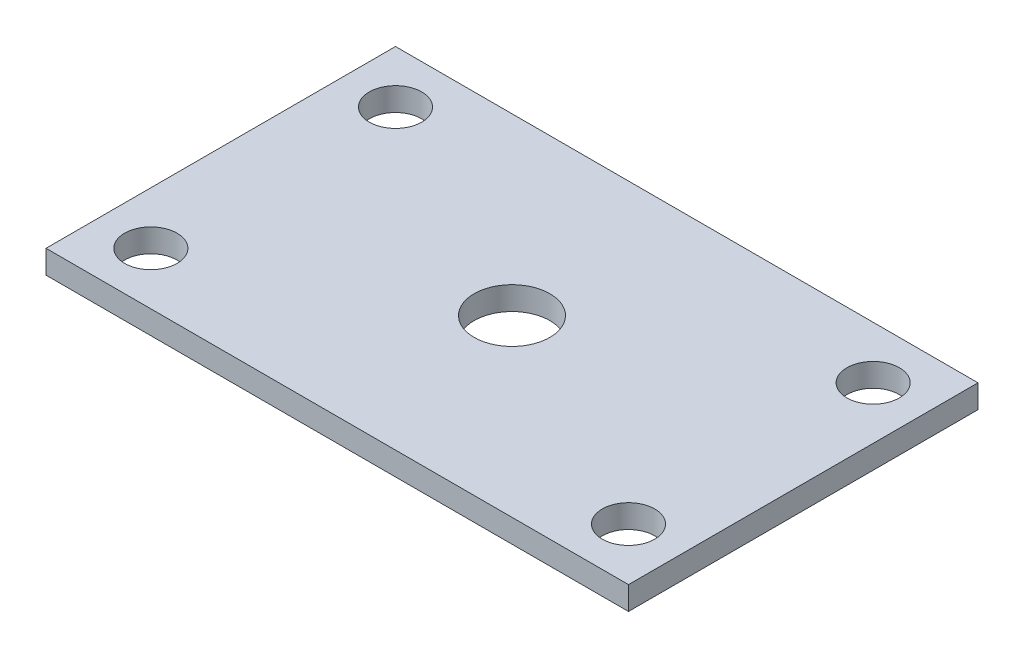
SolidWorks part; units mm, degrees
material "Plain Carbon Steel"
ref_plane "Front Plane" through (0, 0, 0) normal (0, 0, 1) x (1, 0, 0)
ref_plane "Top Plane" through (0, 0, 0) normal (0, 1, 0) x (1, 0, 0)
ref_plane "Right Plane" through (0, 0, 0) normal (1, 0, 0) x (0, 0, -1)
sketch "Sketch1" plane through (0, 0, 0) normal (0, 1, 0) x (1, 0, 0)
  line L1 (-50, -30) -> (50, -30)
  line L2 (-50, -30) -> (-50, 30)
  line L3 (-50, 30) -> (50, 30)
  line L4 (50, -30) -> (50, 30)
  line L5 (-50, -30) -> (50, 30) construction
  line L6 (-50, 30) -> (50, -30) construction
  circle A0 centre (0, 0) radius 6.5
  point P0 (0, 0)
  dimension "D3" = 13
  dimension "D1" = 100
  dimension "D2" = 60
extrude "Boss-Extrude1" add sketch "Sketch1" along normal blind 4
sketch "Sketch2" plane through (0, 4, 0) normal (0, 1, 0) x (1, 0, 0)
  line L0 (0, 32.3584) -> (0, -35.3437) construction
  line L1 (50, 30) -> (-50, 30) construction
  line L2 (-54.8546, 0) -> (67.862, 0) construction
  line L3 (-50, 30) -> (-50, -30) construction
  circle A0 centre (-41, 21) radius 4.5
  circle A1 centre (41, 21) radius 4.5
  circle A2 centre (41, -21) radius 4.5
  circle A3 centre (-41, -21) radius 4.5
  dimension "D1" = 9
  dimension "D3" = 9
  dimension "D2" = 9
extrude "Cut-Extrude1" cut sketch "Sketch2" against normal through all
